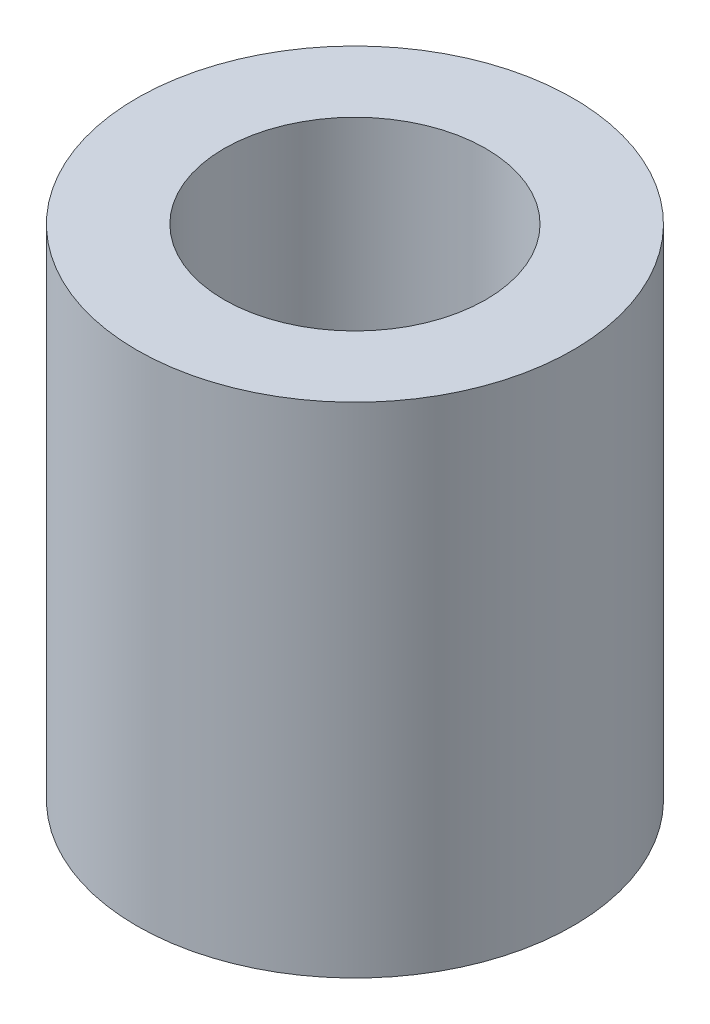
SolidWorks part; units mm, degrees
ref_plane "前视基准面" through (0, 0, 0) normal (0, 0, 1) x (1, 0, 0)
ref_plane "上视基准面" through (0, 0, 0) normal (0, 1, 0) x (1, 0, 0)
ref_plane "右视基准面" through (0, 0, 0) normal (1, 0, 0) x (0, 0, -1)
sketch "草图1" plane through (0, 0, 0) normal (0, 1, 0) x (1, 0, 0)
  circle A0 centre (0, 0) radius 3.5
  circle A1 centre (0, 0) radius 2.1
  dimension "D1" = 7
  dimension "D2" = 4.2
extrude "凸台-拉伸1" add sketch "草图1" along normal blind 8
